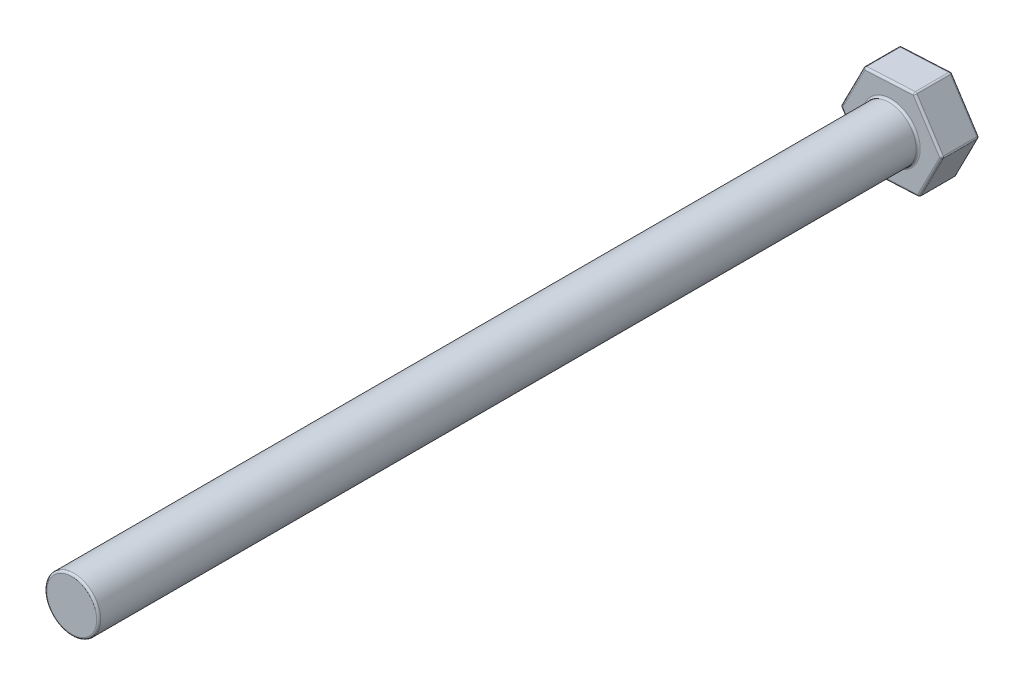
SolidWorks part; units mm, degrees
ref_plane "Спереди" through (0, 0, 0) normal (0, 0, 1) x (1, 0, 0)
ref_plane "Сверху" through (0, 0, 0) normal (0, 1, 0) x (1, 0, 0)
ref_plane "Справа" through (0, 0, 0) normal (1, 0, 0) x (0, 0, -1)
sketch "Эскиз1" plane through (0, 0, 0) normal (0, 0, 1) x (1, 0, 0)
  circle A0 centre (0, 0) radius 3.95
  dimension "D1" = 7.9
extrude "Бобышка-Вытянуть1" add sketch "Эскиз1" along normal blind 120
sketch "Эскиз2" plane through (0, 0, 0) normal (0, 0, -1) x (-1, 0, 0)
  line L1 (-7.4384, 0.3736) -> (-4.0428, -6.2551)
  line L2 (-4.0428, -6.2551) -> (3.3956, -6.6287)
  line L3 (3.3956, -6.6287) -> (7.4384, -0.3736)
  line L4 (7.4384, -0.3736) -> (4.0428, 6.2551)
  line L5 (4.0428, 6.2551) -> (-3.3956, 6.6287)
  line L6 (-3.3956, 6.6287) -> (-7.4384, 0.3736)
  circle A0 centre (0, 0) radius 6.45 construction
  dimension "D1" = 12.9
extrude "Бобышка-Вытянуть2" add sketch "Эскиз2" along normal blind 5.5
fillet "Скругление1" radius 0.3 20 edges at (5.7406, -2.9407, 0) (0.3236, -6.4419, 0) (-5.417, -3.5012, 0) (-5.7406, 2.9407, 0) (-0.3236, 6.4419, 0) (5.417, 3.5012, 0) (-0.3236, 6.4419, -5.5) (-5.7406, 2.9407, -5.5) (-5.417, -3.5012, -5.5) (0.3236, -6.4419, -5.5) (5.7406, -2.9407, -5.5) (5.417, 3.5012, -5.5) (3.95, 0, 0) (3.95, 0, 120) (-3.3956, -6.6287, -2.75) (4.0428, -6.2551, -2.75) (7.4384, 0.3736, -2.75) (3.3956, 6.6287, -2.75) (-7.4384, -0.3736, -2.75) (-4.0428, 6.2551, -2.75)
